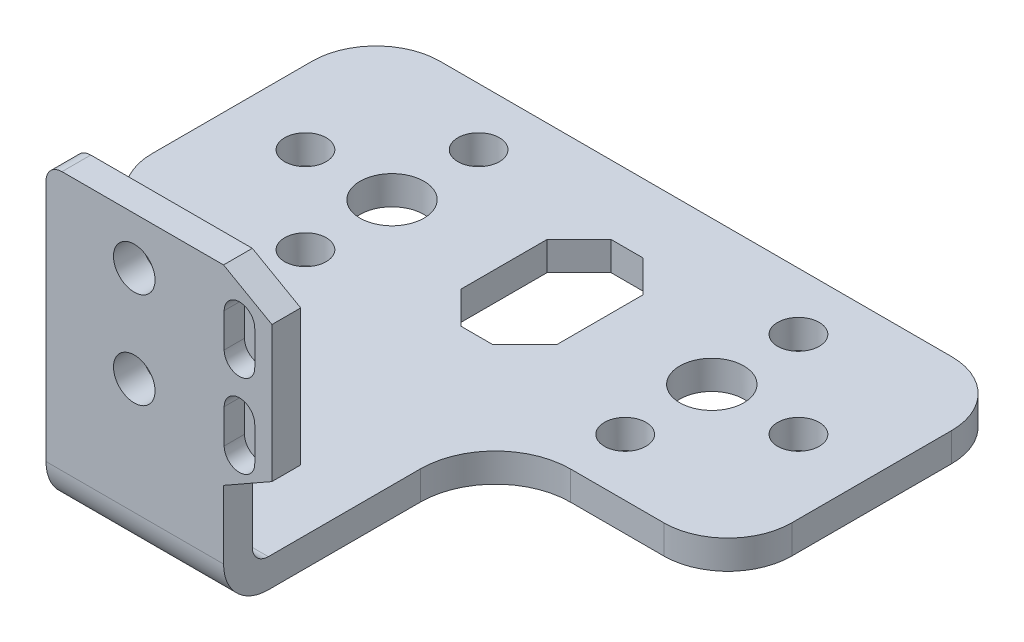
SolidWorks part; units mm, degrees
ref_plane "Front" through (0, 0, 0) normal (0, 0, 1) x (1, 0, 0)
ref_plane "Top" through (0, 0, 0) normal (0, 1, 0) x (1, 0, 0)
ref_plane "Right" through (0, 0, 0) normal (1, 0, 0) x (0, 0, -1)
sketch "Sketch1" plane through (0, 0, 0) normal (1, 0, 0) x (0, 0, -1)
  line L0 (0, 0) -> (0, 45)
  line L1 (0, 45) -> (4.5, 45)
  line L2 (4.5, 45) -> (4.5, 4.5)
  line L3 (4.5, 4.5) -> (90, 4.5)
  line L4 (90, 4.5) -> (90, 0)
  line L5 (90, 0) -> (0, 0)
  dimension "D1" = 4.5
  dimension "D2" = 4.5
  dimension "D3" = 90
  dimension "D4" = 45
extrude "Boss-Extrude1" add sketch "Sketch1" along normal mid plane 100
sketch "Sketch2" plane through (0, 0, 0) normal (0, 1, 0) x (1, 0, 0)
  line L0 (-40, 45) -> (-25.836, 45)
  line L1 (-50, 90) -> (-50, 4.5) construction
  line L2 (50, 90) -> (50, 4.5) construction
  line L4 (-14.0978, 33.2618) -> (-14.0978, 7)
  line L5 (13.6618, 33.2618) -> (13.6618, 7)
  line L7 (50, 90) -> (-50, 90) construction
  line L8 (-2.5, 79.24) -> (2.5, 79.24)
  line L9 (2.5, 79.24) -> (7.5, 74.24)
  line L10 (7.5, 74.24) -> (7.5, 60.76)
  line L11 (7.5, 60.76) -> (2.5, 55.76)
  line L12 (2.5, 55.76) -> (-2.5, 55.76)
  line L13 (-2.5, 55.76) -> (-7.5, 60.76)
  line L14 (-7.5, 60.76) -> (-7.5, 74.24)
  line L15 (-7.5, 74.24) -> (-2.5, 79.24)
  line L16 (-50, 55) -> (-50, 80)
  line L17 (-40, 90) -> (40, 90)
  line L18 (50, 80) -> (50, 55)
  line L19 (25.4, 45) -> (40, 45)
  line L20 (-14.0978, 7) -> (13.6618, 7)
  line L21 (50, 4.5) -> (-50, 4.5) construction
  circle A0 centre (-25, 67.5) radius 5
  circle A1 centre (25, 67.5) radius 5
  circle A2 centre (25, 81.04) radius 3.25
  circle A3 centre (25, 53.96) radius 3.25
  circle A4 centre (38.54, 67.5) radius 3.25
  circle A5 centre (-25, 81.04) radius 3.25
  circle A6 centre (-25, 53.96) radius 3.25
  circle A7 centre (-38.54, 67.5) radius 3.25
  arc A8 (-40, 90) -> (-50, 80) centre (-40, 80) ccw
  arc A9 (40, 90) -> (50, 80) centre (40, 80) cw
  arc A10 (-40, 45) -> (-50, 55) centre (-40, 55) cw
  arc A11 (40, 45) -> (50, 55) centre (40, 55) ccw
  arc A12 (-14.0978, 33.2618) -> (-25.836, 45) centre (-25.836, 33.2618) ccw
  arc A13 (13.6618, 33.2618) -> (25.4, 45) centre (25.4, 33.2618) cw
  point P43 (-50, 90)
  point P47 (50, 90)
  point P52 (-50, 45)
  point P55 (50, 45)
  point P60 (13.6618, 45)
  point P61 (0, 90)
  dimension "D1" = 45
  dimension "D3" = 22.5
  dimension "D14" = 6.5
  dimension "D19" = 10
  dimension "D20" = 10
  dimension "D21" = 11.7382
  dimension "D22" = 11.7382
  dimension "D2" = 22.5
  dimension "D4" = 50
  dimension "D5" = 25
  dimension "D6" = 225
  dimension "D7" = 225
  dimension "D8" = 225
  dimension "D9" = 225
  dimension "D10" = 15
  dimension "D11" = 5
  dimension "D12" = 23.48
  dimension "D13" = 17.5
  dimension "D15" = 13.54
  dimension "D16" = 13.54
  dimension "D17" = 13.54
  dimension "D18" = 13.54
  dimension "D23" = 10.76
  dimension "D24" = 2.5
  dimension "D25" = 14.164
  dimension "D26" = 14.6
  dimension "D27" = 27.7596
extrude "Cut-Extrude34" cut sketch "Sketch2" against normal through all and the other way through all flip side to cut contours L0 A12 L4 L20 L5 A13 L19 A11 L18 A9 L17 A8 L16 A10 | A6 | A0 | A5 | A7 | L10 L11 L12 L13 L14 L15 L8 L9 | A3 | A1 | A2 | A4
sketch "Sketch4" plane through (0, 0, -7) normal (0, 0, 1) x (1, 0, 0)
  line L0 (-14.0978, 0) -> (-14.0978, 45)
  line L1 (-11.5978, 47.5) -> (13.6618, 47.5)
  line L2 (13.6618, 47.5) -> (21.2228, 43.2094)
  line L3 (21.2228, 43.2094) -> (21.2228, 21.944)
  line L4 (21.2228, 21.944) -> (13.6618, 17.6534)
  line L5 (13.6618, 17.6534) -> (13.6618, 4.5)
  line L6 (13.6618, 4.5) -> (13.6618, 0)
  line L7 (13.6618, 0) -> (-14.0978, 0)
  arc A0 (-11.5978, 47.5) -> (-14.0978, 45) centre (-11.5978, 45) ccw
  dimension "D1" = 2.5
  dimension "D2" = 45
extrude "Boss-Extrude3" add sketch "Sketch4" along normal blind 4.5 contours L0 A0 L1 L2 L3 L4 L5 L6 L7
fillet "Fillet3" radius 2.5 1 edges at (-0.218, 4.5, -7)
fillet "Fillet4" radius 7 1 edges at (-0.218, 0, -2.5)
sketch "Sketch6" plane through (0, 0, -2.5) normal (0, 0, 1) x (1, 0, 0)
  line L1 (-14.0978, 7) -> (-14.0978, 45) construction
  circle A0 centre (-0.2978, 40.0831) radius 3.25
  circle A1 centre (-0.2978, 25.0831) radius 3.25
  dimension "D1" = 6.5
  dimension "D2" = 6.5
  dimension "D3" = 15
  dimension "D4" = 13.8
sketch "Sketch7" plane through (0, 0, -2.5) normal (0, 0, 1) x (1, 0, 0)
  line L0 (16.1496, 41.3556) -> (16.1496, 36.0322) construction
  line L1 (18.5396, 41.3556) -> (18.5396, 36.0322)
  line L2 (13.7596, 41.3556) -> (13.7596, 36.0322)
  line L3 (16.1496, 28.3556) -> (16.1496, 23.0322) construction
  line L4 (18.5396, 28.3556) -> (18.5396, 23.0322)
  line L5 (13.7596, 28.3556) -> (13.7596, 23.0322)
  arc A0 (18.5396, 41.3556) -> (13.7596, 41.3556) centre (16.1496, 41.3556) ccw
  arc A1 (13.7596, 36.0322) -> (18.5396, 36.0322) centre (16.1496, 36.0322) ccw
  arc A2 (18.5396, 28.3556) -> (13.7596, 28.3556) centre (16.1496, 28.3556) ccw
  arc A3 (13.7596, 23.0322) -> (18.5396, 23.0322) centre (16.1496, 23.0322) ccw
  point P2 (16.1496, 38.6939)
  point P7 (16.1496, 25.6939)
  dimension "D1" = 4.78
  dimension "D2" = 4.78
  dimension "D3" = 13
extrude "Cut-Extrude35" cut sketch "Sketch6" against normal through all both and the other way through all
extrude "Cut-Extrude39" cut sketch "Sketch7" against normal blind 3.18
